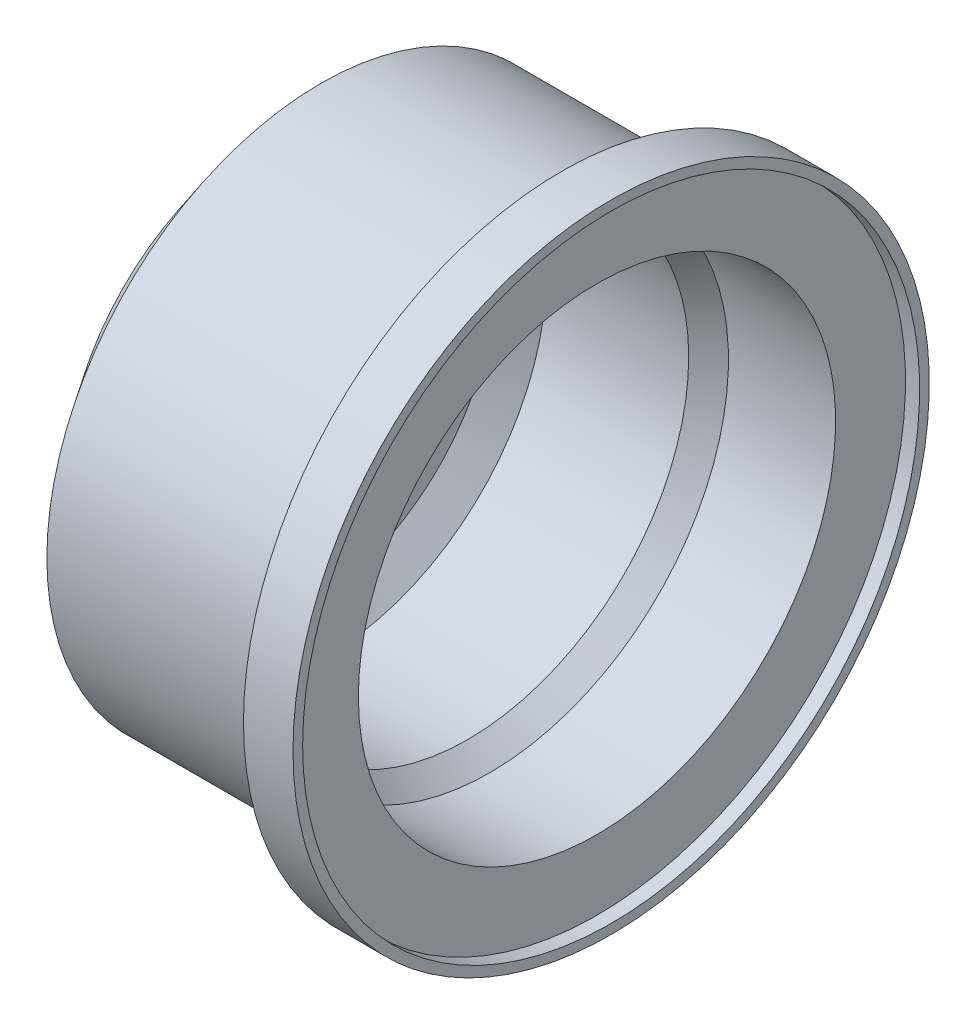
SolidWorks part; units mm, degrees
ref_plane "Front Plane" through (0, 0, 0) normal (0, 0, 1) x (1, 0, 0)
ref_plane "Top Plane" through (0, 0, 0) normal (0, 1, 0) x (1, 0, 0)
ref_plane "Right Plane" through (0, 0, 0) normal (1, 0, 0) x (0, 0, -1)
sketch "Sketch1" plane through (0, 0, 0) normal (0, 0, 1) x (1, 0, 0)
  line L0 (-25, 0) -> (25, 0) construction
  line L2 (-13.622, 15.5) -> (0, 15.5)
  line L3 (0, 15.5) -> (0, 18)
  line L4 (0, 18) -> (2, 18)
  line L5 (2, 17.4531) -> (2, 13.5)
  line L7 (2, 18) -> (2.8, 18)
  line L8 (2.8, 18) -> (2.8, 17.4531)
  line L9 (2.8, 17.4531) -> (2, 17.4531)
  line L10 (-13.622, 15.5) -> (-16.622, 11.5)
  line L11 (-16.622, 11.5) -> (-16.622, 0)
  line L12 (-16.622, 0) -> (-14.622, 0)
  line L13 (2, 13.5) -> (-4.0635, 13.5)
  line L14 (-13.372, 12.5) -> (-14.622, 10.8333)
  line L15 (-14.622, 10.8333) -> (-14.622, 0)
  line L16 (-4.0635, 13.5) -> (-5.311, 12.5)
  line L17 (-5.311, 12.5) -> (-13.372, 12.5)
  dimension "D1" = 50
  dimension "D2" = 25
  dimension "D3" = 1
  dimension "D4" = 2
  dimension "D5" = 2.5
  dimension "D6" = 36
  dimension "D7" = 0.8
  dimension "D8" = 3
  dimension "D9" = 4
  dimension "D10" = 2
  dimension "D11" = 2
  dimension "D12" = 2
revolve "Revolve1" add sketch "Sketch1" angle 360 about L0
sketch "Sketch2" plane through (-16.622, 0, 0) normal (-1, 0, 0) x (0, 0, 1)
  circle A0 centre (0, 0) radius 5
  dimension "D1" = 10
extrude "Cut-Extrude1" cut sketch "Sketch2" against normal blind 10
sketch "Sketch3" plane through (-14.622, 0, 0) normal (1, 0, 0) x (0, 0, -1)
  line L0 (7.1348, 3.0621) -> (7.9756, 3.6339)
  line L1 (0.9156, 7.71) -> (0.8408, 8.724)
  line L2 (0.8408, 8.724) -> (-0.0748, 9.1663)
  line L3 (-0.0748, 9.1663) -> (-0.9156, 8.5945)
  line L4 (-0.9156, 8.5945) -> (-0.8408, 7.5805)
  line L5 (-0.8408, 7.5805) -> (0.0748, 7.1382)
  line L6 (0.0748, 7.1382) -> (0.9156, 7.71)
  line L7 (7.9756, 3.6339) -> (7.9008, 4.6479)
  line L8 (7.9008, 4.6479) -> (6.9853, 5.0901)
  line L9 (6.9853, 5.0901) -> (6.1445, 4.5184)
  line L10 (6.1445, 4.5184) -> (6.2193, 3.5043)
  line L11 (6.2193, 3.5043) -> (7.1348, 3.0621)
  line L12 (6.2193, -4.6479) -> (7.1348, -5.0901)
  line L13 (7.1348, -5.0901) -> (7.9756, -4.5184)
  line L14 (7.9756, -4.5184) -> (7.9008, -3.5043)
  line L15 (7.9008, -3.5043) -> (6.9853, -3.0621)
  line L16 (6.9853, -3.0621) -> (6.1445, -3.6339)
  line L17 (6.1445, -3.6339) -> (6.2193, -4.6479)
  line L18 (-0.9156, -7.71) -> (-0.8408, -8.724)
  line L19 (-0.8408, -8.724) -> (0.0748, -9.1663)
  line L20 (0.0748, -9.1663) -> (0.9156, -8.5945)
  line L21 (0.9156, -8.5945) -> (0.8408, -7.5805)
  line L22 (0.8408, -7.5805) -> (-0.0748, -7.1382)
  line L23 (-0.0748, -7.1382) -> (-0.9156, -7.71)
  line L24 (-7.1348, -3.0621) -> (-7.9756, -3.6339)
  line L25 (-7.9756, -3.6339) -> (-7.9008, -4.6479)
  line L26 (-7.9008, -4.6479) -> (-6.9853, -5.0901)
  line L27 (-6.9853, -5.0901) -> (-6.1445, -4.5184)
  line L28 (-6.1445, -4.5184) -> (-6.2193, -3.5043)
  line L29 (-6.2193, -3.5043) -> (-7.1348, -3.0621)
  line L30 (-6.2193, 4.6479) -> (-7.1348, 5.0901)
  line L31 (-7.1348, 5.0901) -> (-7.9756, 4.5184)
  line L32 (-7.9756, 4.5184) -> (-7.9008, 3.5043)
  line L33 (-7.9008, 3.5043) -> (-6.9853, 3.0621)
  line L34 (-6.9853, 3.0621) -> (-6.1445, 3.6339)
  line L35 (-6.1445, 3.6339) -> (-6.2193, 4.6479)
  circle A0 centre (0, 0) radius 8.1522 construction
  circle A1 centre (0, 8.1522) radius 0.8806 construction
  point P44 (0, 0)
  dimension "D1" = 6
extrude "Boss-Extrude1" add sketch "Sketch3" along normal blind 0.5
